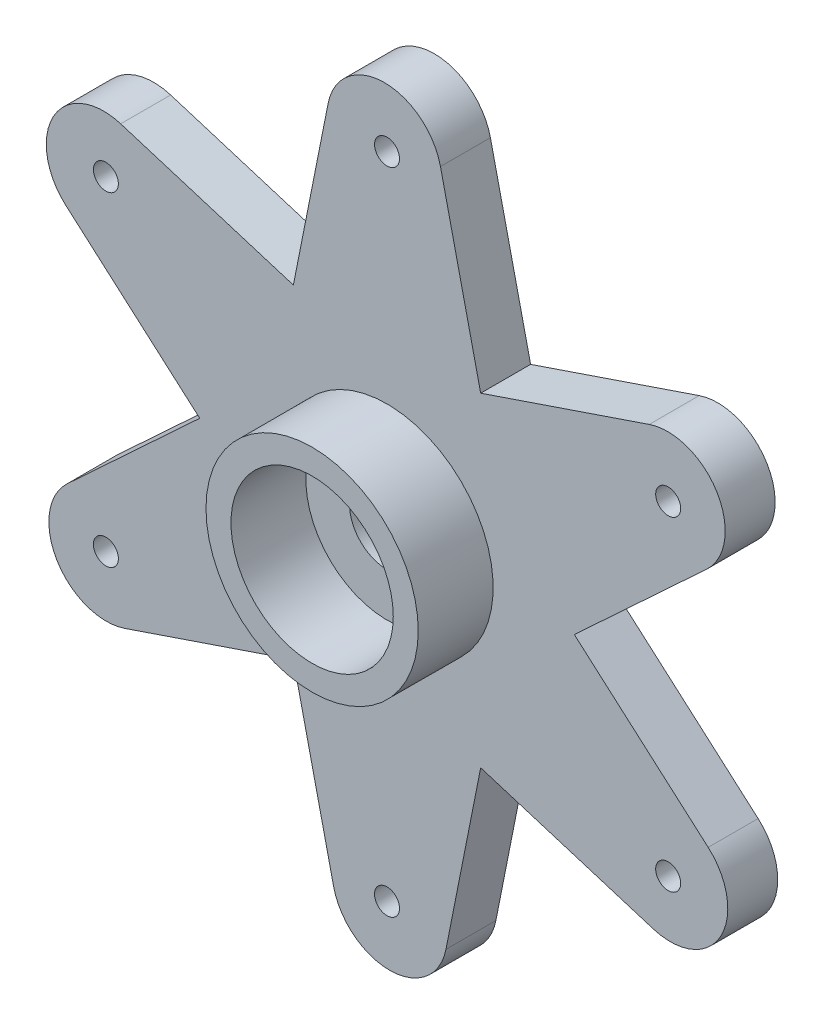
SolidWorks part; units mm, degrees
ref_plane "Plano frontal" through (0, 0, 0) normal (0, 0, 1) x (1, 0, 0)
ref_plane "Plano superior" through (0, 0, 0) normal (0, 1, 0) x (1, 0, 0)
ref_plane "Plano direito" through (0, 0, 0) normal (1, 0, 0) x (0, 0, -1)
sketch "Esboço1" plane through (0, 0, 0) normal (0, 0, 1) x (1, 0, 0)
  line L0 (3.75, 6.4952) -> (2.1402, 13.5512)
  line L1 (-3.75, 6.4952) -> (-2.3598, 13.4881)
  line L2 (7.5, 0) -> (12.8058, 4.9221)
  line L3 (3.75, 6.4952) -> (10.5011, 8.7877)
  line L4 (3.75, -6.4952) -> (10.6656, -8.6291)
  line L5 (7.5, 0) -> (12.8609, -4.7004)
  line L6 (-3.75, -6.4952) -> (-2.1402, -13.5512)
  line L7 (3.75, -6.4952) -> (2.3598, -13.4881)
  line L8 (-7.5, 0) -> (-12.8058, -4.9221)
  line L9 (-3.75, -6.4952) -> (-10.5011, -8.7877)
  line L10 (-3.75, 6.4952) -> (-10.6656, 8.6291)
  line L11 (-7.5, 0) -> (-12.8609, 4.7004)
  arc A1 (-2.3598, 13.4881) -> (2.1402, 13.5512) centre (-0.1031, 13.0394) cw
  arc A2 (10.5011, 8.7877) -> (12.8058, 4.9221) centre (11.2409, 6.609) cw
  arc A3 (12.8609, -4.7004) -> (10.6656, -8.6291) centre (11.344, -6.4305) cw
  arc A4 (2.3598, -13.4881) -> (-2.1402, -13.5512) centre (0.1031, -13.0394) cw
  arc A5 (-10.5011, -8.7877) -> (-12.8058, -4.9221) centre (-11.2409, -6.609) cw
  arc A6 (-12.8609, 4.7004) -> (-10.6656, 8.6291) centre (-11.344, 6.4305) cw
  circle A7 centre (0, 0) radius 1.5
  point P36 (0, 0)
  dimension "D2" = 7.5
  dimension "D5" = 3
  dimension "D3" = 4.5
  dimension "D4" = 6
extrude "Ressalto-extrusão1" add sketch "Esboço1" along normal mid plane 2
sketch "Esboço2" plane through (0, 0, 1) normal (0, 0, 1) x (1, 0, 0)
  circle A0 centre (0, 0) radius 4.25
  circle A1 centre (0, 0) radius 3.25
  dimension "D1" = 8.5
  dimension "D2" = 6.5
extrude "Ressalto-extrusão2" add sketch "Esboço2" along normal blind 3
sketch "Esboço3" plane through (0, 0, 1) normal (0, 0, 1) x (1, 0, 0)
  circle A0 centre (0, 0) radius 13
  circle A1 centre (0, 13) radius 0.5
  circle A2 centre (11.2583, 6.5) radius 0.5
  circle A3 centre (11.2583, -6.5) radius 0.5
  circle A4 centre (0, -13) radius 0.5
  circle A5 centre (-11.2583, -6.5) radius 0.5
  circle A6 centre (-11.2583, 6.5) radius 0.5
  point P17 (0, 0)
  dimension "D1" = 1
  dimension "D2" = 26
  dimension "D3" = 6
extrude "Corte-extrusão1" cut sketch "Esboço3" against normal blind 2 contours A1 | A6 | A5 | A4 | A3 | A2
